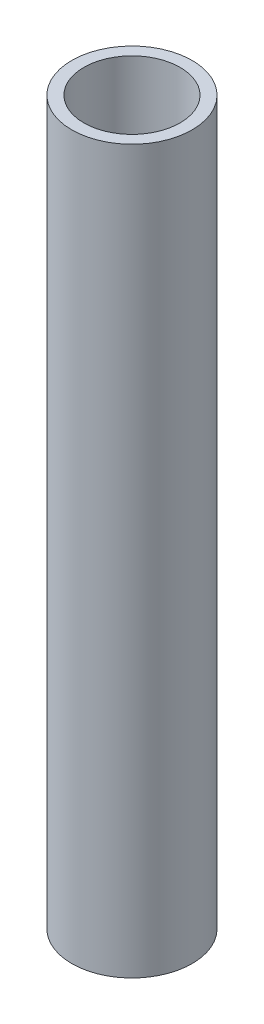
SolidWorks part; units mm, degrees
ref_plane "Front Plane" through (0, 0, 0) normal (0, 0, 1) x (1, 0, 0)
ref_plane "Top Plane" through (0, 0, 0) normal (0, 1, 0) x (1, 0, 0)
ref_plane "Right Plane" through (0, 0, 0) normal (1, 0, 0) x (0, 0, -1)
sketch "MDS_base" plane through (0, 0, 0) normal (0, 1, 0) x (1, 0, 0)
  line L0 (30.3464, 52.5614) -> (-60.6927, 0) construction
  line L1 (-60.6927, 0) -> (30.3464, -52.5614) construction
  line L2 (30.3464, -52.5614) -> (30.3464, 52.5614) construction
  line L3 (30.3464, 52.5614) -> (0, 0) construction
  line L4 (0, 0) -> (30.3464, -52.5614) construction
  line L5 (0, 0) -> (-60.6927, 0) construction
  circle A0 centre (0, 0) radius 60.6927 construction
  dimension "D1" = 60.6927
sketch "Sketch2" plane through (0, 0, 0) normal (0, 1, 0) x (1, 0, 0)
  circle A0 centre (30.3464, 52.5614) radius 5
  circle A1 centre (30.3464, 52.5614) radius 4
  dimension "D1" = 10
  dimension "D2" = 1
extrude "Boss-Extrude1" add sketch "Sketch2" along normal blind 60
